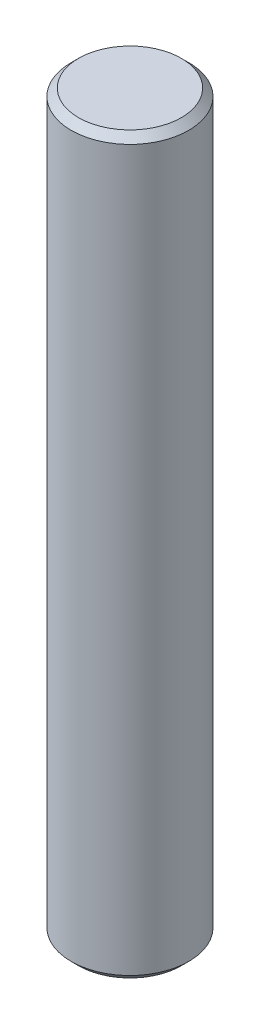
SolidWorks part; units mm, degrees
ref_plane "Front Plane" through (0, 0, 0) normal (0, 0, 1) x (1, 0, 0)
ref_plane "Top Plane" through (0, 0, 0) normal (0, 1, 0) x (1, 0, 0)
ref_plane "Right Plane" through (0, 0, 0) normal (1, 0, 0) x (0, 0, -1)
sketch "Sketch2" plane through (0, 0, 0) normal (0, 1, 0) x (1, 0, 0)
  circle A0 centre (0, 0) radius 4
extrude "Boss-Extrude1" add sketch "Sketch2" along normal blind 50
chamfer "Chamfer1" distance 0.5 angle 45 2 edges at (0, 50, 4) (0, 0, 4)
